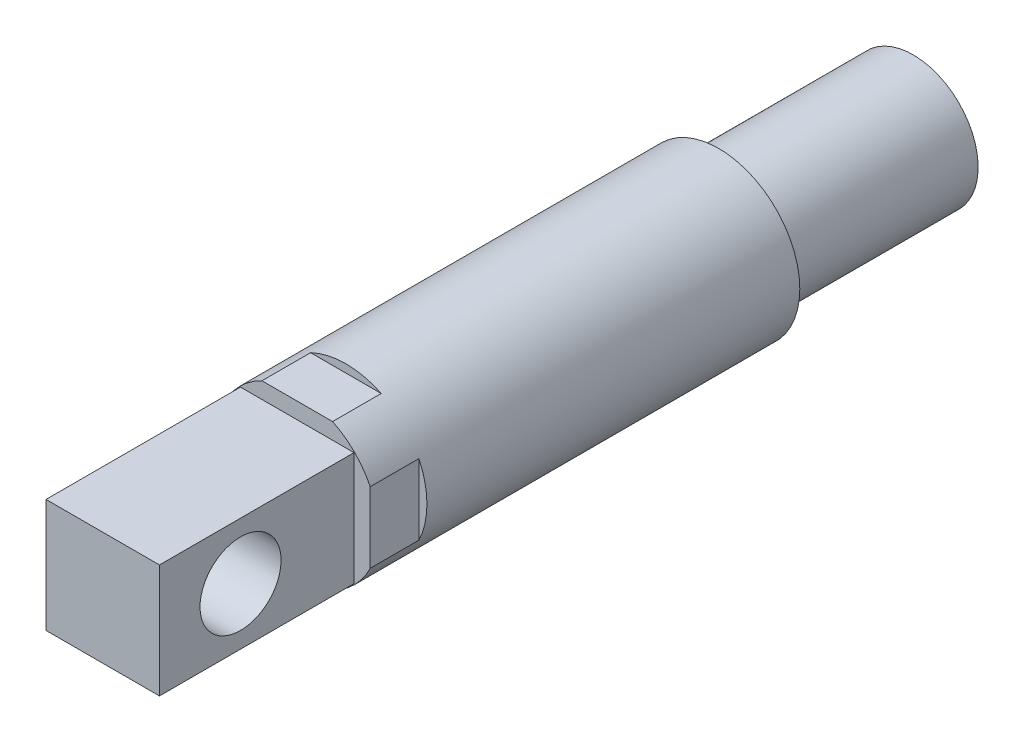
SolidWorks part; units mm, degrees
material "ABS"
ref_plane "Plan de face" through (0, 0, 0) normal (0, 0, 1) x (1, 0, 0)
ref_plane "Plan de dessus" through (0, 0, 0) normal (0, 1, 0) x (1, 0, 0)
ref_plane "Plan de droite" through (0, 0, 0) normal (1, 0, 0) x (0, 0, -1)
sketch "Esquisse1" plane through (0, 0, 0) normal (0, 0, 1) x (1, 0, 0)
  circle A0 centre (0, 0) radius 5
  dimension "D1" = 10
extrude "Boss.-Extru.2" add sketch "Esquisse1" along normal blind 70
sketch "Esquisse2" plane through (0, 0, 0) normal (0, 0, -1) x (-1, 0, 0)
  circle A0 centre (0, 0) radius 3.5
  dimension "D1" = 7
extrude "Boss.-Extru.3" add sketch "Esquisse2" along normal blind 12
sketch "Esquisse4" plane through (0, 0, 70) normal (0, 0, 1) x (1, 0, 0)
  circle A0 centre (0, 0) radius 15
  dimension "D1" = 30
extrude "Boss.-Extru.5" add sketch "Esquisse4" against normal blind 5
sketch "Esquisse5" plane through (0, 0, 70) normal (0, 0, 1) x (1, 0, 0)
  circle A0 centre (0, 0) radius 3.5
  dimension "D1" = 7
extrude "Boss.-Extru.6" add sketch "Esquisse5" along normal blind 12
sketch "Esquisse6" plane through (0, 0, 70) normal (0, 0, 1) x (1, 0, 0)
  line L0 (0, 10) -> (0, -10) construction
  line L1 (-10, 0) -> (10, 0) construction
  line L2 (0, 10) -> (0, 15) construction
  line L3 (10, 0) -> (15, 0) construction
  line L4 (15, 0) -> (-15, 0) construction
  line L5 (0, -10) -> (0, -15) construction
  line L6 (0, 15) -> (1.425, 9.8979)
  line L7 (0, 15) -> (-1.425, 9.8979)
  line L8 (0, 0) -> (-3.8907, 14.5215) construction
  line L9 (0, 0) -> (-7.5126, 13.022) construction
  line L10 (0, 0) -> (-10.6237, 10.6372) construction
  line L11 (0, 0) -> (-13.0125, 7.5291) construction
  line L12 (0, 0) -> (-14.5165, 3.9092) construction
  line L13 (-3.8907, 14.5215) -> (-1.1901, 9.9289)
  line L14 (-3.8907, 14.5215) -> (-3.9427, 9.19)
  line L15 (-7.4994, 12.9907) -> (-6.1827, 7.8596)
  line L16 (-7.4994, 12.9907) -> (-3.7145, 9.2845)
  line L17 (-14.5165, 3.9092) -> (-9.1849, 3.9543)
  line L18 (-14.5165, 3.9092) -> (-9.9274, 1.2028)
  line L19 (-10.6237, 10.6372) -> (-7.9997, 6.0004)
  line L20 (-10.6237, 10.6372) -> (-5.9821, 8.0134)
  line L21 (-12.9812, 7.516) -> (-7.8518, 6.1927)
  line L22 (-12.9812, 7.516) -> (-9.2798, 3.7263)
  line L23 (-15, 0.0191) -> (-9.8961, 1.4376)
  line L24 (-15, 0.0191) -> (-9.8998, -1.4124)
  line L25 (-15, -0.0191) -> (-9.8961, -1.4376)
  line L26 (-14.5165, -3.9092) -> (-9.9274, -1.2028)
  line L27 (-14.5165, -3.9092) -> (-9.1849, -3.9543)
  line L28 (-12.9812, -7.516) -> (-9.2798, -3.7263)
  line L29 (-12.9812, -7.516) -> (-7.8518, -6.1927)
  line L30 (-10.6237, -10.6372) -> (-7.9997, -6.0004)
  line L31 (-10.6237, -10.6372) -> (-5.9821, -8.0134)
  line L32 (-7.4994, -12.9907) -> (-6.1827, -7.8596)
  line L33 (-7.4994, -12.9907) -> (-3.7145, -9.2845)
  line L34 (-3.8907, -14.5215) -> (-3.9427, -9.19)
  line L35 (-3.8907, -14.5215) -> (-1.1901, -9.9289)
  line L36 (0, -15) -> (-1.425, -9.8979)
  line L37 (0, -15) -> (1.425, -9.8979)
  line L38 (3.8907, -14.5215) -> (1.1901, -9.9289)
  line L39 (3.8907, -14.5215) -> (3.9427, -9.19)
  line L40 (7.4994, -12.9907) -> (3.7145, -9.2845)
  line L41 (7.4994, -12.9907) -> (6.1827, -7.8596)
  line L42 (10.6237, -10.6372) -> (5.9821, -8.0134)
  line L43 (10.6237, -10.6372) -> (7.9997, -6.0004)
  line L44 (12.9812, -7.516) -> (7.8518, -6.1927)
  line L45 (12.9812, -7.516) -> (9.2798, -3.7263)
  line L46 (14.5165, -3.9092) -> (9.1849, -3.9543)
  line L47 (14.5165, -3.9092) -> (9.9274, -1.2028)
  line L48 (15, 0.0191) -> (9.8998, -1.4124)
  line L49 (15, 0.0191) -> (9.8961, 1.4376)
  line L50 (14.5165, 3.9092) -> (9.9274, 1.2028)
  line L51 (14.5165, 3.9092) -> (9.1849, 3.9543)
  line L52 (12.9812, 7.516) -> (9.2798, 3.7263)
  line L53 (12.9812, 7.516) -> (7.8518, 6.1927)
  line L54 (10.6237, 10.6372) -> (7.9997, 6.0004)
  line L55 (10.6237, 10.6372) -> (5.9821, 8.0134)
  line L56 (7.4994, 12.9907) -> (6.1827, 7.8596)
  line L57 (7.4994, 12.9907) -> (3.7145, 9.2845)
  line L58 (0, 15) -> (1.425, 9.8979)
  line L59 (3.8907, 14.5215) -> (3.9427, 9.19)
  line L60 (3.8907, 14.5215) -> (1.1901, 9.9289)
  circle A0 centre (0, 0) radius 10
  circle A1 centre (0, 0) radius 15 construction
  circle A2 centre (0, 0) radius 15.0337
  circle M35 centre (0, 0) radius 15
  dimension "D3" = 1.425
  dimension "D4" = 3.92
  dimension "D8" = 3.92
  dimension "D9" = 2.85
  dimension "D10" = 1.43
extrude "Enlèv. mat.-Extru.1" cut sketch "Esquisse6" against normal blind 12 contours L20 L15 M35 | L21 L19 M35 | L22 L17 M35 | L23 L18 M35 | L26 L25 M35 | L28 L27 M35 | L30 L29 M35 | L32 L31 M35 | L34 L33 M35 | L36 L35 M35 | L38 L37 M35 | L40 L39 M35 | L42 L41 M35 | L44 L43 M35 | L46 L45 M35 | L48 L47 M35 | L50 L49 M35 | L52 L51 M35 | L54 L53 M35 | L56 L55 M35 | L59 L57 M35 | L60 L6 M35 | L13 L7 M35 | L16 L14 M35
sketch "Esquisse7" plane through (0, 0, 82) normal (0, 0, 1) x (1, 0, 0)
  circle A0 centre (0, 0) radius 15
extrude "Enlèv. mat.-Extru.2" cut sketch "Esquisse7" against normal blind 47
sketch "Esquisse8" plane through (0, 0, 35) normal (0, 0, 1) x (1, 0, 0)
  line L1 (-4.5, -4.5) -> (4.5, -4.5)
  line L2 (-4.5, -4.5) -> (-4.5, 4.5)
  line L3 (-4.5, 4.5) -> (4.5, 4.5)
  line L4 (4.5, -4.5) -> (4.5, 4.5)
  line L5 (-4.5, -4.5) -> (4.5, 4.5) construction
  line L6 (-4.5, 4.5) -> (4.5, -4.5) construction
  point P0 (0, 0)
  dimension "D1" = 9
  dimension "D2" = 9
extrude "Boss.-Extru.7" add sketch "Esquisse8" against normal blind 5
sketch "Esquisse9" plane through (0, 0, 35) normal (0, 0, 1) x (1, 0, 0)
  line L1 (-4.5, -4.5) -> (4.5, -4.5)
  line L2 (-4.5, -4.5) -> (-4.5, 4.5)
  line L3 (-4.5, 4.5) -> (4.5, 4.5)
  line L4 (4.5, -4.5) -> (4.5, 4.5)
  line L5 (-4.5, -4.5) -> (4.5, 4.5) construction
  line L6 (-4.5, 4.5) -> (4.5, -4.5) construction
  line L7 (-5, -5) -> (5, -5)
  line L8 (-5, -5) -> (-5, 5)
  line L9 (-5, 5) -> (5, 5)
  line L10 (5, -5) -> (5, 5)
  line L11 (-5, -5) -> (5, 5) construction
  line L12 (-5, 5) -> (5, -5) construction
  point P0 (0, 0)
  point P7 (0, 0)
  dimension "D1" = 10
  dimension "D2" = 10
extrude "Enlèv. mat.-Extru.3" cut sketch "Esquisse9" against normal blind 12
sketch "Esquisse10" plane through (0, 0, 35) normal (0, 0, 1) x (1, 0, 0)
  line L1 (-4.5, -4.5) -> (4.5, -4.5)
  line L2 (-4.5, -4.5) -> (-4.5, 4.5)
  line L3 (-4.5, 4.5) -> (4.5, 4.5)
  line L4 (4.5, -4.5) -> (4.5, 4.5)
  line L5 (-4.5, -4.5) -> (4.5, 4.5) construction
  line L6 (-4.5, 4.5) -> (4.5, -4.5) construction
  point P0 (0, 0)
extrude "Boss.-Extru.8" add sketch "Esquisse10" along normal blind 7
sketch "Esquisse11" plane through (0, 0, 42) normal (0, 0, 1) x (1, 0, 0)
  line L1 (-4.5, 4.5) -> (4.5, 4.5)
  line L2 (-4.5, 4.5) -> (-4.5, -4.5)
  line L3 (-4.5, -4.5) -> (4.5, -4.5)
  line L4 (4.5, 4.5) -> (4.5, -4.5)
  line L5 (-4.5, 4.5) -> (4.5, -4.5) construction
  line L6 (-4.5, -4.5) -> (4.5, 4.5) construction
  point P0 (0, 0)
extrude "Enlèv. mat.-Extru.4" cut sketch "Esquisse11" against normal blind 4
sketch "Esquisse13" plane through (0, 0, 38) normal (0, 0, 1) x (1, 0, 0)
  line L1 (-4.5, 4.5) -> (4.5, 4.5)
  line L2 (-4.5, 4.5) -> (-4.5, -4.5)
  line L3 (-4.5, -4.5) -> (4.5, -4.5)
  line L4 (4.5, 4.5) -> (4.5, -4.5)
  line L5 (-4.5, 4.5) -> (4.5, -4.5) construction
  line L6 (-4.5, -4.5) -> (4.5, 4.5) construction
  point P0 (0, 0)
extrude "Boss.-Extru.9" add sketch "Esquisse13" against normal blind 12
sketch "Esquisse14" plane through (0, 0, 38) normal (0, 0, 1) x (1, 0, 0)
  line L1 (-3.5, 3.5) -> (3.5, 3.5)
  line L2 (-3.5, 3.5) -> (-3.5, -3.5)
  line L3 (-3.5, -3.5) -> (3.5, -3.5)
  line L4 (3.5, 3.5) -> (3.5, -3.5)
  line L5 (-3.5, 3.5) -> (3.5, -3.5) construction
  line L6 (-3.5, -3.5) -> (3.5, 3.5) construction
  line L7 (-4.5, 4.5) -> (4.5, 4.5)
  line L8 (-4.5, 4.5) -> (-4.5, -4.5)
  line L9 (-4.5, -4.5) -> (4.5, -4.5)
  line L10 (4.5, 4.5) -> (4.5, -4.5)
  line L11 (-4.5, 4.5) -> (4.5, -4.5) construction
  line L12 (-4.5, -4.5) -> (4.5, 4.5) construction
  point P0 (0, 0)
  point P6 (0, 0)
  dimension "D1" = 7
  dimension "D2" = 7
extrude "Enlèv. mat.-Extru.5" cut sketch "Esquisse14" against normal blind 12
sketch "Esquisse15" plane through (3.5, 0, 0) normal (1, 0, 0) x (0, 0, -1)
  line L0 (-38, -3.5) -> (-38, 3.5) construction
  circle A0 centre (-33, 0) radius 2.5
  dimension "D1" = 5
  dimension "D2" = 5
extrude "Enlèv. mat.-Extru.6" cut sketch "Esquisse15" against normal blind 12
sketch "Esquisse16" plane through (0, 0, -12) normal (0, 0, -1) x (-1, 0, 0)
  circle A0 centre (0, 0) radius 4
  dimension "D1" = 8
extrude "Boss.-Extru.10" add sketch "Esquisse16" against normal blind 12
